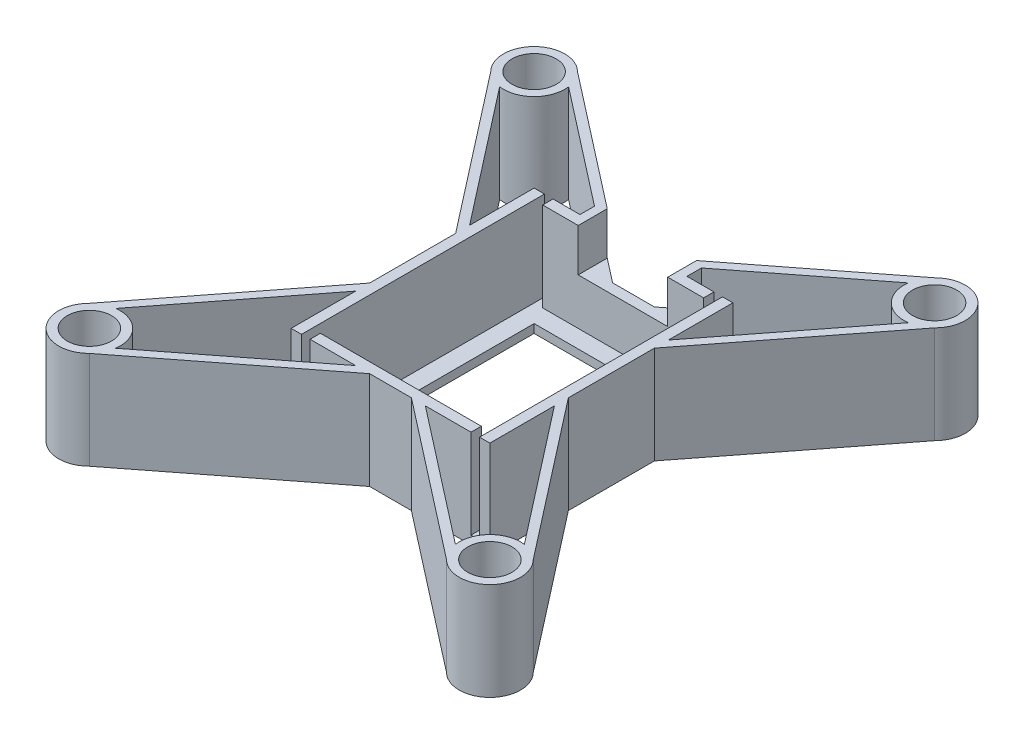
SolidWorks part; units mm, degrees
ref_plane "Front Plane" through (0, 0, 0) normal (0, 0, 1) x (1, 0, 0)
ref_plane "Top Plane" through (0, 0, 0) normal (0, 1, 0) x (1, 0, 0)
ref_plane "Right Plane" through (0, 0, 0) normal (1, 0, 0) x (0, 0, -1)
sketch "Sketch1" plane through (0, 0, 0) normal (0, 1, 0) x (1, 0, 0)
  line L1 (-12.56, 16.0886) -> (15.3, 16.0886)
  line L2 (-12.56, 16.0886) -> (-12.56, -17.9714)
  line L3 (-12.56, -17.9714) -> (15.3, -17.9714)
  line L4 (15.3, 16.0886) -> (15.3, -17.9714)
  line L8 (-26.7021, 30.2307) -> (-12.56, 16.0886) construction
  line L9 (1.37, 38.2305) -> (1.37, -32.1505) construction
  line L10 (-25.448, -0.9414) -> (31.3507, -0.9414) construction
  line L11 (26.402, 33.2717) -> (4.3, 16.0886)
  line L12 (-29.7423, 27.1898) -> (-12.56, 5.0886)
  line L13 (-23.662, 33.2717) -> (-1.56, 16.0886)
  line L14 (-27.2731, 25.9688) -> (-12.56, 7.0437)
  line L15 (-22.4402, 30.8018) -> (-3.5151, 16.0886)
  line L16 (-28.7949, 27.9263) -> (-11.6126, 5.8251) construction
  line L17 (-24.3985, 32.3243) -> (-2.2965, 15.1412) construction
  line L19 (25.1802, 30.8018) -> (6.2551, 16.0886)
  line L20 (32.4823, 27.1898) -> (15.3, 5.0886)
  line L21 (30.0131, 25.9688) -> (15.3, 7.0437)
  line L22 (-23.662, -35.1545) -> (-1.56, -17.9714)
  line L23 (-22.4402, -32.6847) -> (-3.5151, -17.9714)
  line L24 (-27.2731, -27.8516) -> (-12.56, -8.9265)
  line L25 (-29.7423, -29.0726) -> (-12.56, -6.9714)
  line L26 (32.4823, -29.0726) -> (15.3, -6.9714)
  line L27 (30.0131, -27.8516) -> (15.3, -8.9265)
  line L29 (25.1802, -32.6847) -> (6.2551, -17.9714)
  line L30 (-25.0035, -34.8915) -> (-24.9596, -34.8569)
  line L31 (26.402, -35.1545) -> (4.3, -17.9714)
  line L32 (29.4422, 30.2307) -> (15.3, 16.0886) construction
  circle A1 centre (-26.7021, 30.2307) radius 3.1
  arc A2 (-27.2731, 25.9688) -> (-22.4402, 30.8018) centre (-26.7021, 30.2307) ccw
  circle A3 centre (-26.7021, 30.2307) radius 4.3 construction
  arc A4 (-23.662, 33.2717) -> (-29.7423, 27.1898) centre (-26.7021, 30.2307) ccw
  arc A5 (26.402, 33.2717) -> (32.4823, 27.1898) centre (29.4422, 30.2307) cw
  arc A6 (30.0131, 25.9688) -> (25.1802, 30.8018) centre (29.4422, 30.2307) cw
  circle A7 centre (29.4422, 30.2307) radius 3.1
  arc A8 (-27.2731, -27.8516) -> (-22.4402, -32.6847) centre (-26.7021, -32.1136) cw
  circle A9 centre (-26.7021, -32.1136) radius 3.1
  arc A10 (-23.662, -35.1545) -> (-29.7423, -29.0726) centre (-26.7021, -32.1136) cw
  circle A11 centre (29.4422, -32.1136) radius 3.1
  arc A12 (30.0131, -27.8516) -> (25.1802, -32.6847) centre (29.4422, -32.1136) ccw
  arc A13 (26.402, -35.1545) -> (32.4823, -29.0726) centre (29.4422, -32.1136) ccw
  point P4 (-1.56, 16.0886)
  point P5 (-12.56, 5.0886)
  point P11 (-26.7021, 30.2307)
  point P13 (-26.7021, 30.2307)
  point P18 (-26.7021, 30.2307)
  point P26 (-26.7021, 30.2307)
  point P41 (29.4422, 30.2307)
  point P42 (29.4422, 30.2307)
  point P43 (29.4422, 30.2307)
  point P44 (29.4422, 30.2307)
  point P64 (-26.7021, -32.1136)
  point P65 (-26.7021, -32.1136)
  point P66 (-26.7021, -32.1136)
  point P71 (29.4422, -32.1136)
  point P72 (29.4422, -32.1136)
  point P73 (29.4422, -32.1136)
  point P74 (29.4422, -32.1136)
  dimension "D6" = 6.2
  dimension "D10" = 135
  dimension "D5" = 1.2
  dimension "D1" = 27.86
  dimension "D2" = 34.06
  dimension "D3" = 11
  dimension "D4" = 11
  dimension "D7" = 135
  dimension "D8" = 1.2
  dimension "D9" = 1.2
extrude "Boss-Extrude4" add sketch "Sketch1" along normal blind 13.7
sketch "Sketch6" plane through (0, 13.7, 0) normal (0, 1, 0) x (1, 0, 0)
  line L0 (-11.11, 14.6386) -> (-11.11, -16.5214)
  line L5 (-11.11, -16.5214) -> (13.85, -16.5214)
  line L6 (13.85, 14.6386) -> (13.85, -16.5214)
  line L7 (-11.11, 14.6386) -> (13.85, 14.6386)
extrude "Cut-Extrude1" cut sketch "Sketch6" against normal blind 12.5
sketch "Sketch7" plane through (0, 1.2, 0) normal (0, 1, 0) x (1, 0, 0)
  line L8 (11.35, 12.1386) -> (-8.61, 12.1386)
  line L9 (-8.61, 12.1386) -> (-8.61, -14.0214)
  line L10 (-8.61, -14.0214) -> (11.35, -14.0214)
  line L11 (11.35, -14.0214) -> (11.35, 12.1386)
  line L12 (11.35, 12.1386) -> (-8.61, 12.1386)
  line L13 (-8.61, 12.1386) -> (-8.61, -14.0214)
  line L14 (-8.61, -14.0214) -> (11.35, -14.0214)
  line L15 (11.35, -14.0214) -> (11.35, 12.1386)
  dimension "D1" = 2.5
extrude "Cut-Extrude2" cut sketch "Sketch7" against normal blind 12.5
sketch "Sketch9" plane through (0, 0, -14.6386) normal (0, 0, 1) x (1, 0, 0)
  line L0 (13.85, 13.7) -> (-11.11, 13.7) construction
  line L1 (-11.11, 1.2) -> (-9.91, 1.2)
  line L2 (-11.11, 1.2) -> (-11.11, 13.7)
  line L3 (-11.11, 13.7) -> (-9.91, 13.7)
  line L4 (-9.91, 1.2) -> (-9.91, 13.7)
  line L6 (13.85, 1.2) -> (12.65, 1.2)
  line L7 (13.85, 1.2) -> (13.85, 13.7)
  line L8 (13.85, 13.7) -> (12.65, 13.7)
  line L9 (12.65, 1.2) -> (12.65, 13.7)
  dimension "D1" = 1.2
  dimension "D2" = 1.2
extrude "Cut-Extrude3" cut sketch "Sketch9" against normal up to surface (1.45 mm away) up to face at (-8.0375, 6.85, -16.0886)
sketch "Sketch10" plane through (0, 0, 16.5214) normal (0, 0, -1) x (-1, 0, 0)
  line L0 (11.11, 13.7) -> (-13.85, 13.7) construction
  line L1 (-13.85, 1.2) -> (-12.65, 1.2)
  line L2 (-13.85, 1.2) -> (-13.85, 13.7)
  line L3 (-13.85, 13.7) -> (-12.65, 13.7)
  line L4 (-12.65, 1.2) -> (-12.65, 13.7)
  line L6 (11.11, 1.2) -> (9.91, 1.2)
  line L7 (11.11, 1.2) -> (11.11, 13.7)
  line L8 (11.11, 13.7) -> (9.91, 13.7)
  line L9 (9.91, 1.2) -> (9.91, 13.7)
  dimension "D1" = 1.2
  dimension "D2" = 1.2
extrude "Cut-Extrude4" cut sketch "Sketch10" against normal up to surface (1.45 mm away) up to face at (10.7776, 6.85, 17.9714)
sketch "Sketch11" plane through (0, 0, 0) normal (0, -1, 0) x (1, 0, 0)
  line L0 (1.37, 35.7933) -> (1.37, -26.5232) construction
  line L1 (-26.881, -29.5611) -> (-26.0325, -30.4096)
  line L2 (-26.881, -29.5611) -> (-22.9947, -25.6747)
  line L3 (-26.0325, -30.4096) -> (-22.1461, -26.5232)
  line L4 (-22.1461, -26.5232) -> (-22.9947, -25.6747)
  line L5 (-25.0044, 0.9414) -> (26.0382, 0.9414) construction
  line L6 (24.8862, -26.5232) -> (25.7347, -25.6747)
  line L7 (28.7725, -30.4096) -> (24.8862, -26.5232)
  line L8 (29.6211, -29.5611) -> (25.7347, -25.6747)
  line L9 (29.6211, -29.5611) -> (28.7725, -30.4096)
  line L10 (29.6211, 31.4439) -> (28.7725, 32.2925)
  line L11 (29.6211, 31.4439) -> (25.7347, 27.5576)
  line L12 (28.7725, 32.2925) -> (24.8862, 28.4061)
  line L13 (24.8862, 28.4061) -> (25.7347, 27.5576)
  line L14 (-22.1461, 28.4061) -> (-22.9947, 27.5576)
  line L15 (-26.0325, 32.2925) -> (-22.1461, 28.4061)
  line L16 (-26.881, 31.4439) -> (-22.9947, 27.5576)
  line L17 (-26.881, 31.4439) -> (-26.0325, 32.2925)
  point P6 (-26.4568, -29.9853)
  point P14 (29.1968, -29.9853)
  point P23 (29.1968, 31.8682)
  point P24 (-26.4568, 31.8682)
  dimension "D1" = 1.2
extrude "Cut-Extrude5" cut sketch "Sketch11" against normal blind 1.5
sketch "Sketch12" plane through (0, 0, -14.6386) normal (0, 0, 1) x (1, 0, 0)
  line L0 (12.65, 13.7) -> (-9.91, 13.7) construction
  line L2 (1.37, 13.7) -> (-6.13, 13.7)
  line L3 (1.37, 13.7) -> (1.37, 7.7)
  line L4 (1.37, 7.7) -> (-6.13, 7.7)
  line L5 (-6.13, 13.7) -> (-6.13, 7.7)
  line L6 (1.37, 13.7) -> (8.87, 13.7)
  line L7 (1.37, 13.7) -> (1.37, 7.7)
  line L8 (1.37, 7.7) -> (8.87, 7.7)
  line L9 (8.87, 13.7) -> (8.87, 7.7)
  point P0 (1.37, 13.7)
  line M3 (12.65, 13.7) -> (-9.91, 13.7)
  dimension "D1" = 6
  dimension "D2" = 7.5
  dimension "D3" = 7.5
extrude "Cut-Extrude6" cut sketch "Sketch12" against normal through all contours L5 L4 L3 M3 | L9 L3 L8 M3
sketch "Sketch14" plane through (0, 7.7, 0) normal (0, 1, 0) x (1, 0, 0)
  line L0 (-6.13, 19.6415) -> (-6.13, 14.6386)
  line L1 (-6.13, 14.6386) -> (-4.93, 14.6386)
  line L2 (8.87, 14.6386) -> (-6.13, 14.6386) construction
  line L3 (-4.93, 14.6386) -> (-4.93, 18.7086)
  line L4 (-6.13, 19.6415) -> (-1.56, 16.0886) construction
  line L5 (-4.93, 18.7086) -> (-6.13, 19.6415)
  line L6 (8.87, 19.6415) -> (8.87, 14.6386)
  line L7 (12.65, 14.6386) -> (-9.91, 14.6386) construction
  line L8 (8.87, 14.6386) -> (7.622, 14.6386)
  line L9 (7.622, 14.6386) -> (7.622, 18.6713)
  line L10 (8.87, 19.6415) -> (4.3, 16.0886) construction
  line L11 (7.622, 18.6713) -> (8.87, 19.6415)
  dimension "D1" = 1.2
extrude "Boss-Extrude5" add sketch "Sketch14" along normal up to vertex (6 mm away)
sketch "Sketch15" plane through (0, 7.7, 0) normal (0, -1, 0) x (1, 0, 0)
  line L0 (-6.13, -16.0886) -> (-6.13, -18.1215)
  line L1 (-6.13, -18.1215) -> (-3.5151, -16.0886)
  line L2 (-3.5151, -16.0886) -> (-6.13, -16.0886)
  line L3 (8.87, -16.0886) -> (8.87, -18.1215)
  line L4 (25.1802, -30.8018) -> (6.2551, -16.0886) construction
  line L5 (8.87, -16.0886) -> (8.87, -18.1215) construction
  line L6 (8.87, -18.1215) -> (6.2551, -16.0886)
  line L7 (6.2551, -16.0886) -> (8.87, -16.0886)
extrude "Boss-Extrude6" add sketch "Sketch15" along normal up to vertex (7.7 mm away)
